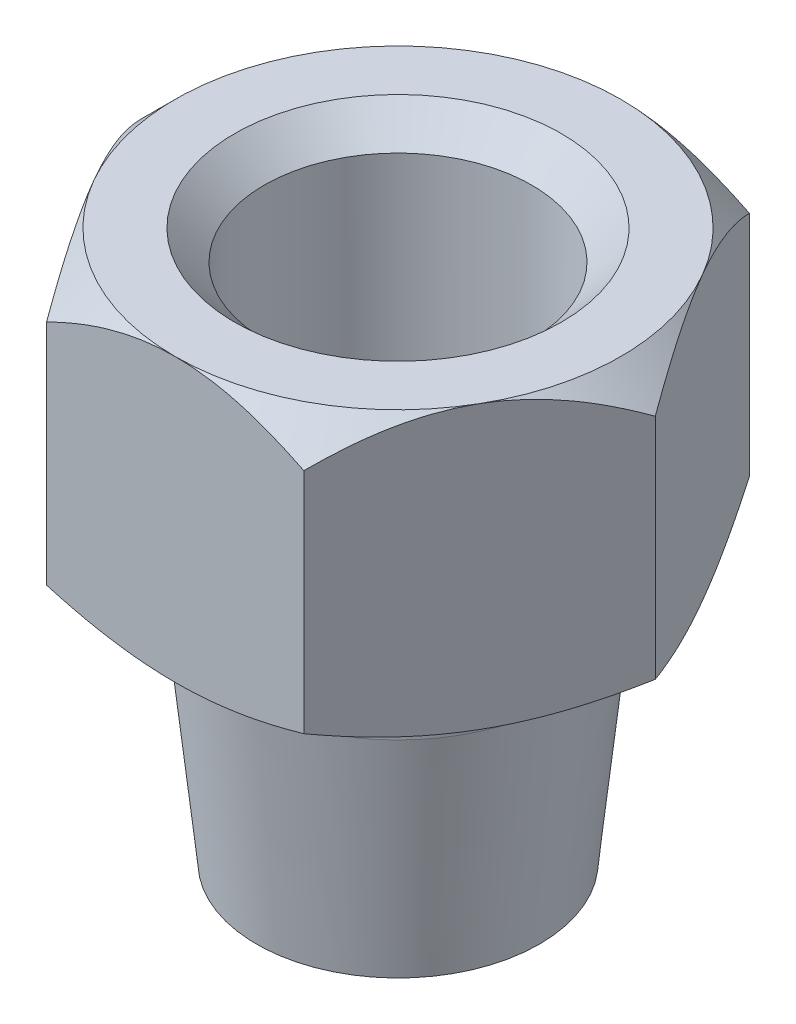
SolidWorks part; units mm, degrees
ref_plane "Alzado" through (0, 0, 0) normal (0, 0, 1) x (1, 0, 0)
ref_plane "Planta" through (0, 0, 0) normal (0, 1, 0) x (1, 0, 0)
ref_plane "Vista lateral" through (0, 0, 0) normal (1, 0, 0) x (0, 0, -1)
sketch "Croquis1" plane through (0, 0, 0) normal (0, 0, 1) x (1, 0, 0)
  line L0 (0, 51.9305) -> (0, -46.2059) construction
  line L1 (6.35, 31.3792) -> (20, 31.3792)
  line L2 (22, 29.3792) -> (22, 14.3792)
  line L3 (20, 12.3792) -> (14, 12.3792)
  line L4 (11.11, 9.3792) -> (9.525, -5.6208)
  line L5 (9.525, -5.6208) -> (1.5875, -5.6208)
  line L6 (6.35, 31.3792) -> (6.35, 12.3792)
  line L7 (14, 12.3792) -> (11.11, 12.3792)
  line L8 (11.11, 12.3792) -> (11.11, 9.3792)
  line L9 (20, 12.3792) -> (22, 12.3792)
  line L10 (22, 12.3792) -> (22, 14.3792)
  line L11 (20, 31.3792) -> (22, 31.3792)
  line L12 (22, 31.3792) -> (22, 29.3792)
  line L13 (6.35, 12.3792) -> (1.5875, 12.3792)
  line L14 (1.5875, 12.3792) -> (1.5875, -5.6208)
  point P4 (22, 31.3792)
  point P6 (22, 12.3792)
  dimension "D3" = 15
  dimension "D12" = 11.11
  dimension "D2" = 22
  dimension "D6" = 18
  dimension "D7" = 15
  dimension "D8" = 1.5875
  dimension "D9" = 22
  dimension "D10" = 6.35
  dimension "D11" = 19
  dimension "D13" = 9.525
revolve "Revolución1" add sketch "Croquis1" angle 360 about L0
sketch "Croquis4" plane through (0, 31.3792, 0) normal (0, 1, 0) x (1, 0, 0)
  line L1 (17.3205, 0) -> (8.6603, 15)
  line L2 (8.6603, 15) -> (-8.6603, 15)
  line L3 (-8.6603, 15) -> (-17.3205, 0)
  line L4 (-17.3205, 0) -> (-8.6603, -15)
  line L5 (-8.6603, -15) -> (8.6603, -15)
  line L6 (8.6603, -15) -> (17.3205, 0)
  circle A0 centre (0, 0) radius 15 construction
  dimension "D1" = 30
extrude "Cortar-Extruir6" cut sketch "Croquis4" against normal blind 70 flip side to cut
sketch "Croquis5" plane through (0, 31.3792, 0) normal (0, 1, 0) x (1, 0, 0)
  circle A0 centre (0, 0) radius 15
  dimension "D1" = 30
extrude "Cortar-Extruir7" cut sketch "Croquis5" against normal blind 70 draft 45 flip side to cut
sketch "Croquis6" plane through (0, 31.3792, 0) normal (0, 1, 0) x (1, 0, 0)
  circle A0 centre (0, 0) radius 9
  dimension "D1" = 18
extrude "Cortar-Extruir8" cut sketch "Croquis6" against normal blind 15
chamfer "Chaflán1" distance 2 angle 45 1 edges at (-9, 31.3792, 0)
fillet "Redondeo1" radius 1 1 edges at (-6.35, 16.3792, 0)
sketch "Croquis7" plane through (0, 12.3792, 0) normal (0, -1, 0) x (1, 0, 0)
  circle A0 centre (0, 0) radius 15
  dimension "D1" = 30
extrude "Cortar-Extruir9" cut sketch "Croquis7" against normal blind 10 draft 60 flip side to cut
